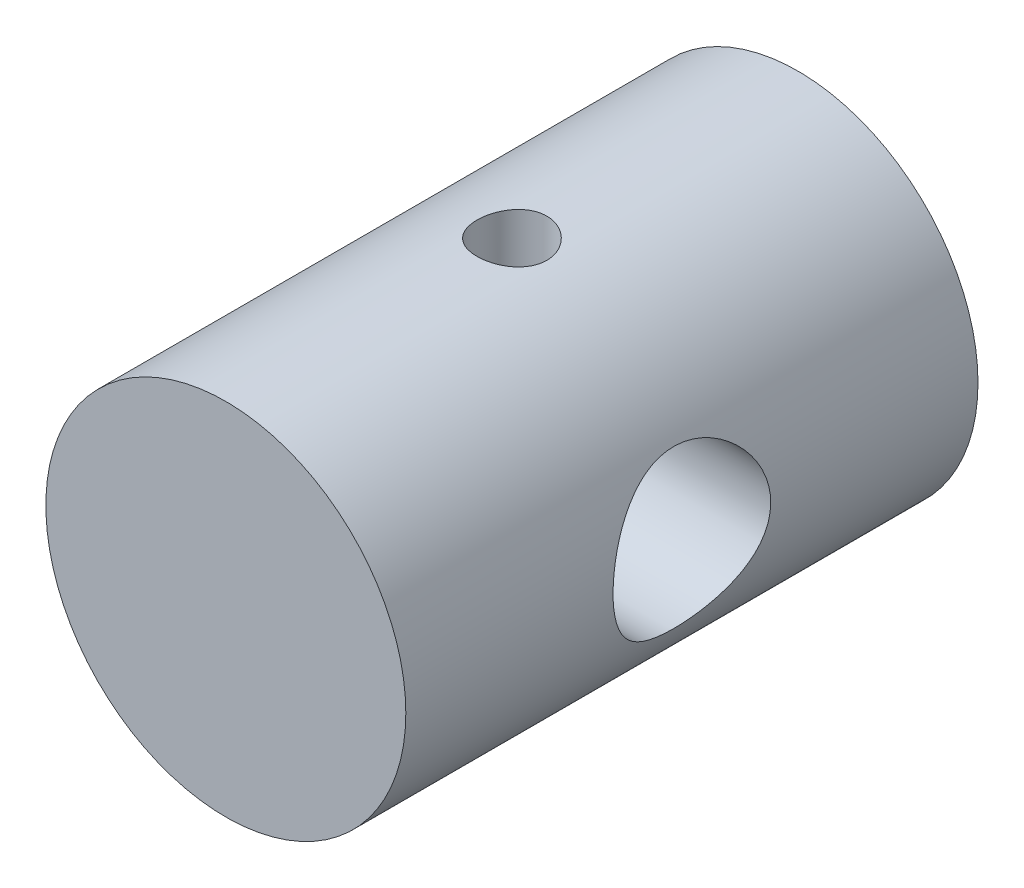
SolidWorks part; units mm, degrees
ref_plane "Front" through (0, 0, 0) normal (0, 0, 1) x (1, 0, 0)
ref_plane "Top" through (0, 0, 0) normal (0, 1, 0) x (1, 0, 0)
ref_plane "Right" through (0, 0, 0) normal (1, 0, 0) x (0, 0, -1)
sketch "Sketch1" plane through (0, 0, 0) normal (0, 0, 1) x (1, 0, 0)
  circle A0 centre (0, 0) radius 7.99
extrude "Extrude1" add sketch "Sketch1" along normal blind 25.4
sketch "Sketch2" plane through (0, 0, 0) normal (1, 0, 0) x (0, 0, -1)
  circle A0 centre (-12.7, 0) radius 3.5
extrude "Cut-Extrude2" cut sketch "Sketch2" against normal through all and the other way through all contours A0
sketch "Sketch3" plane through (0, 0, 0) normal (0, 1, 0) x (1, 0, 0)
  line L0 (-7.99, -12.7) -> (7.99, -12.7) construction
  circle A0 centre (0, -12.7) radius 1.55
extrude "Cut-Extrude3" cut sketch "Sketch3" against normal through all and the other way through all contours A0
